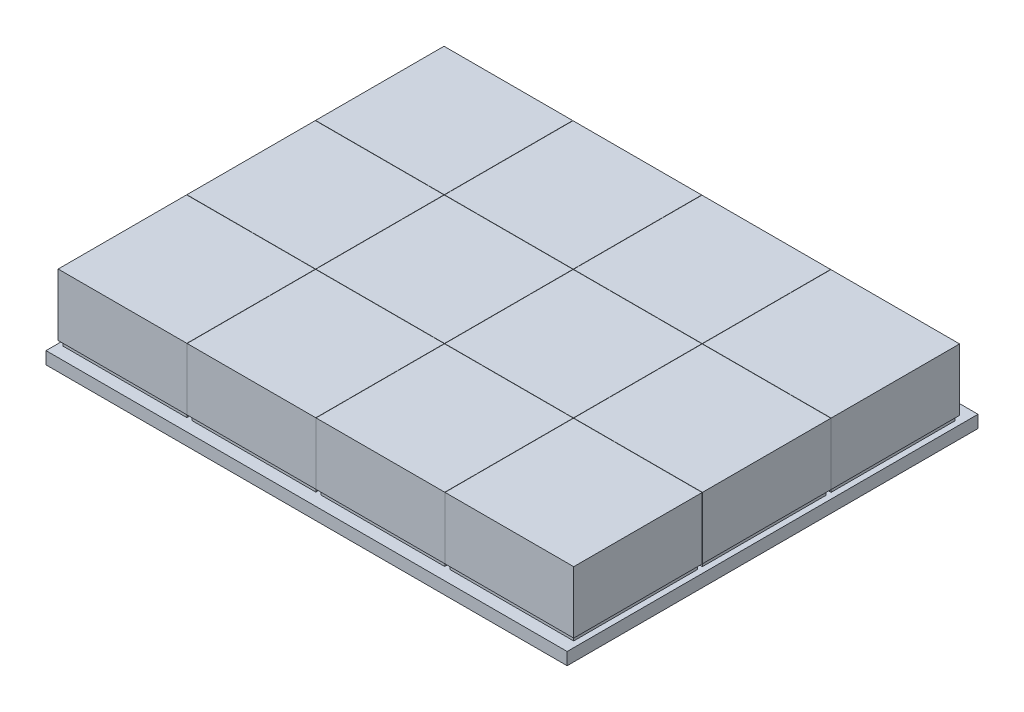
SolidWorks part; units mm, degrees
ref_plane "Front Plane" through (0, 0, 0) normal (0, 0, 1) x (1, 0, 0)
ref_plane "Top Plane" through (0, 0, 0) normal (0, 1, 0) x (1, 0, 0)
ref_plane "Right Plane" through (0, 0, 0) normal (1, 0, 0) x (0, 0, -1)
sketch "Sketch1" plane through (0, 0, 0) normal (0, 1, 0) x (1, 0, 0)
  line L1 (-250, -83) -> (250, -83)
  line L2 (-250, -83) -> (-250, 83)
  line L3 (-250, 83) -> (250, 83)
  line L4 (250, -83) -> (250, 83)
  line L5 (-250, -83) -> (250, 83) construction
  line L6 (-250, 83) -> (250, -83) construction
  point P0 (0, 0)
  dimension "D1" = 500
  dimension "D2" = 166
extrude "Boss-Extrude1" add sketch "Sketch1" along normal blind 5
sketch "Sketch2" plane through (0, 5, 0) normal (0, 1, 0) x (1, 0, 0)
  line L0 (0, 0) -> (0, -83) construction
  line L1 (-250, -83) -> (250, -83) construction
  line L3 (-25, -28) -> (25, -28)
  line L4 (-25, -28) -> (-25, -78)
  line L5 (-25, -78) -> (25, -78)
  line L6 (25, -28) -> (25, -78)
  line L7 (-25, -28) -> (25, -78) construction
  line L8 (-25, -78) -> (25, -28) construction
  point P5 (0, -53)
  dimension "D1" = 50
  dimension "D2" = 50
  dimension "D3" = 5
extrude "Boss-Extrude3" add sketch "Sketch2" along normal blind 2
pattern_linear "LPattern1" count 3 spacing 52 along (0, 0, -1) of "Boss-Extrude3"
sketch "Sketch3" plane through (0, 7, 0) normal (0, 1, 0) x (1, 0, 0)
  line L0 (0, 0) -> (0, -78) construction
  line L1 (-25, -78) -> (25, -78) construction
  line L3 (-26, -27.1) -> (26, -27.1)
  line L4 (-26, -27.1) -> (-26, -79)
  line L5 (-26, -79) -> (26, -79)
  line L6 (26, -27.1) -> (26, -79)
  line L7 (-26, -27.1) -> (26, -79) construction
  line L8 (-26, -79) -> (26, -27.1) construction
  line L9 (-250, -83) -> (250, -83) construction
  point P5 (0, -53.05)
  dimension "D1" = 52
  dimension "D2" = 51.9
  dimension "D3" = 4
extrude "Boss-Extrude8" add sketch "Sketch3" along normal blind 25
pattern_linear "LPattern5" count 3 spacing 52 along (0, 0, -1) of "Boss-Extrude8"
pattern_linear "LPattern6" count 4 spacing 52.1 along (1, 0, 0) of "Boss-Extrude3", "LPattern1", "Boss-Extrude8", "LPattern5"
sketch "Sketch4" plane through (0, 5, 0) normal (0, 1, 0) x (1, 0, 0)
  line L0 (250, 83) -> (-250, 83) construction
  line L1 (-26.9101, 83) -> (-250, 83)
  line L2 (-26.9101, 83) -> (-26.9101, -83)
  line L3 (-26.9101, -83) -> (-250, -83)
  line L4 (-250, 83) -> (-250, -83)
  line L6 (250, -83) -> (183.6449, -83)
  line L7 (250, -83) -> (250, 83)
  line L8 (250, 83) -> (183.6449, 83)
  line L9 (183.6449, -83) -> (183.6449, 83)
extrude "Cut-Extrude1" cut sketch "Sketch4" against normal blind 10
